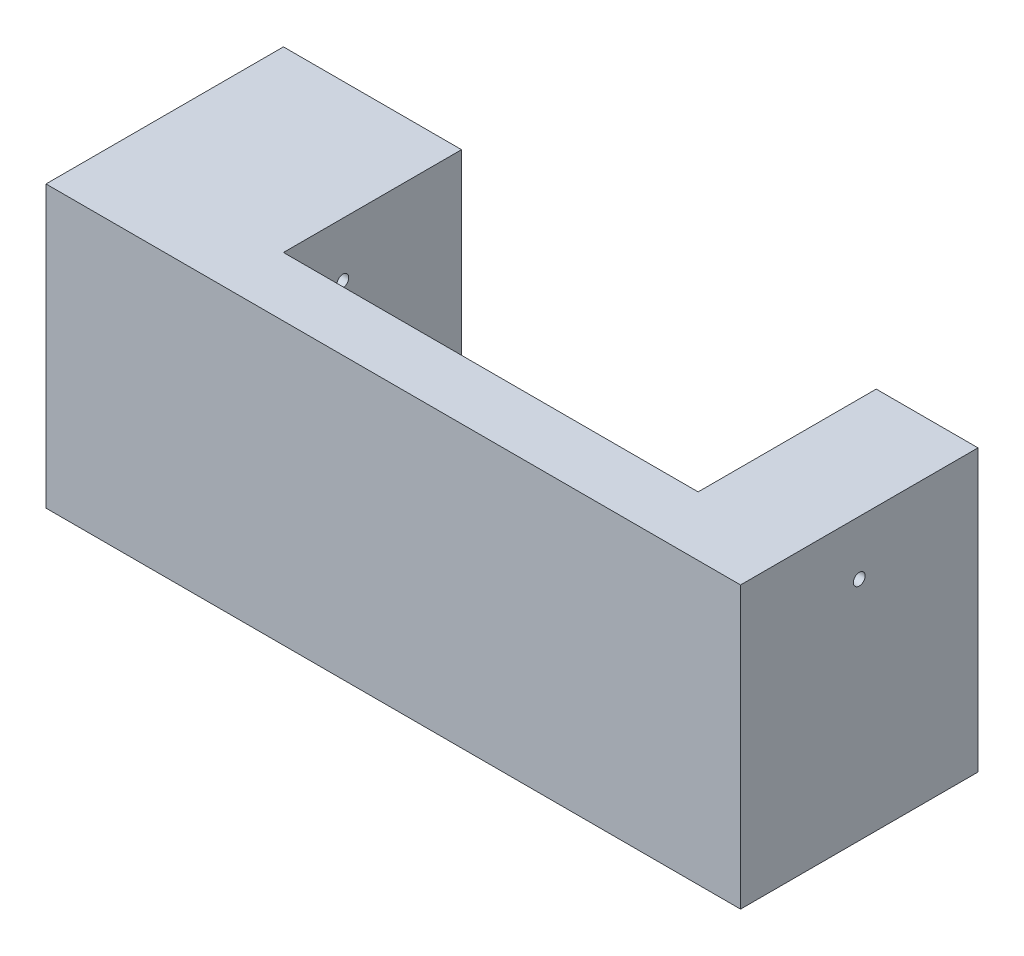
SolidWorks part; units mm, degrees
ref_plane "Alzado" through (0, 0, 0) normal (0, 0, 1) x (1, 0, 0)
ref_plane "Planta" through (0, 0, 0) normal (0, 1, 0) x (1, 0, 0)
ref_plane "Vista lateral" through (0, 0, 0) normal (1, 0, 0) x (0, 0, -1)
sketch "Croquis1" plane through (0, 0, 0) normal (1, 0, 0) x (0, 0, -1)
  line L0 (0, 55) -> (0, -55) construction
  line L1 (-20, -23.65) -> (20, -23.65)
  line L2 (-20, -23.65) -> (-20, 23.65)
  line L3 (-20, 23.65) -> (20, 23.65)
  line L4 (20, -23.65) -> (20, 23.65)
  line L5 (-20, -23.65) -> (20, 23.65) construction
  line L6 (-20, 23.65) -> (20, -23.65) construction
  circle A0 centre (0, 14.4893) radius 1
  point P0 (0, 0)
  dimension "D2" = 2
  dimension "D1" = 47.3
  dimension "D3" = 40
extrude "Saliente-Extruir1" add sketch "Croquis1" along normal blind 30
sketch "Croquis2" plane through (30, 0, 0) normal (1, 0, 0) x (0, 0, -1)
  line L0 (-20, -23.65) -> (20, -23.65) construction
  line L1 (-20, 23.65) -> (-10, 23.65)
  line L2 (-20, 23.65) -> (-20, -23.65)
  line L3 (-20, -23.65) -> (-10, -23.65)
  line L4 (-10, 23.65) -> (-10, -23.65)
  dimension "D1" = 10
extrude "Saliente-Extruir2" add sketch "Croquis2" along normal blind 87
sketch "Croquis3" plane through (0, 0, 10) normal (0, 0, -1) x (-1, 0, 0)
  line L0 (-30, -23.65) -> (-30, 23.65) construction
  line L1 (-117, 23.65) -> (-99.854, 23.65)
  line L2 (-117, 23.65) -> (-117, -23.65)
  line L3 (-117, -23.65) -> (-99.854, -23.65)
  line L4 (-99.854, 23.65) -> (-99.854, -23.65)
extrude "Saliente-Extruir3" add sketch "Croquis3" along normal blind 30
sketch "Croquis4" plane through (0, 0, 0) normal (-1, 0, 0) x (0, 0, 1)
  circle A0 centre (0, 14.4893) radius 1
extrude "Cortar-Extruir1" cut sketch "Croquis4" against normal through all
